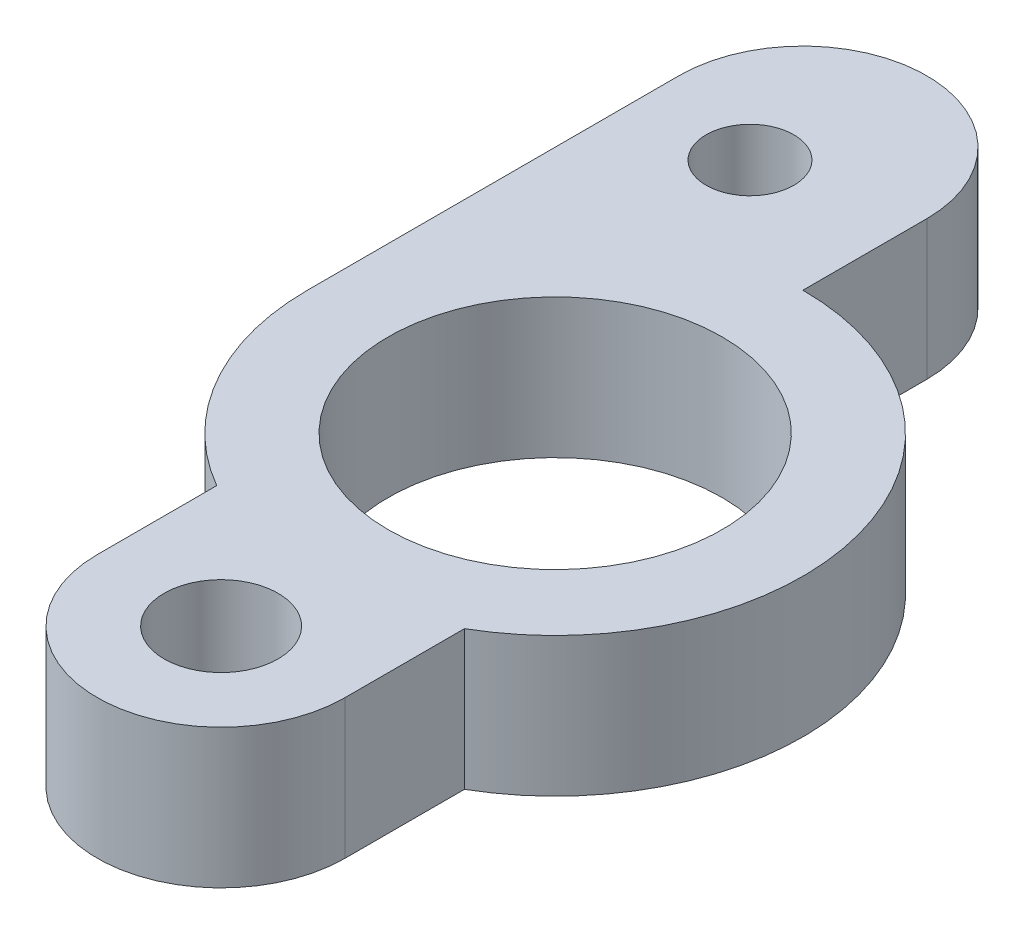
SolidWorks part; units mm, degrees
ref_plane "Front Plane" through (0, 0, 0) normal (0, 0, 1) x (1, 0, 0)
ref_plane "Top Plane" through (0, 0, 0) normal (0, 1, 0) x (1, 0, 0)
ref_plane "Right Plane" through (0, 0, 0) normal (1, 0, 0) x (0, 0, -1)
sketch "Sketch1" plane through (0, 0, 0) normal (0, 1, 0) x (1, 0, 0)
  line L1 (-11.303, 16.9545) -> (-11.303, 0)
  line L2 (0, 16.9545) -> (0, 11.303)
  line L4 (-5.6515, -9.7887) -> (-5.6515, -15.24)
  line L6 (5.6515, -9.7887) -> (5.6515, -15.24)
  arc A0 (-11.303, 0) -> (-5.6515, -9.7887) centre (0, 0) ccw
  circle A1 centre (0, 0) radius 7.62
  arc A2 (0, 16.9545) -> (-11.303, 16.9545) centre (-5.6515, 16.9545) ccw
  circle A3 centre (-6.35, 15.24) radius 2
  circle A4 centre (0, -15.24) radius 2.5979
  arc A5 (-5.6515, -15.24) -> (5.6515, -15.24) centre (0, -15.24) ccw
  arc A6 (5.6515, -9.7887) -> (0, 11.303) centre (0, 0) ccw
  dimension "D1" = 22.606
  dimension "D2" = 15.24
  dimension "D6" = 4
  dimension "D7" = 6.35
  dimension "D5" = 15.24
  dimension "D8" = 15.24
extrude "Boss-Extrude1" add sketch "Sketch1" along normal blind 6.35
